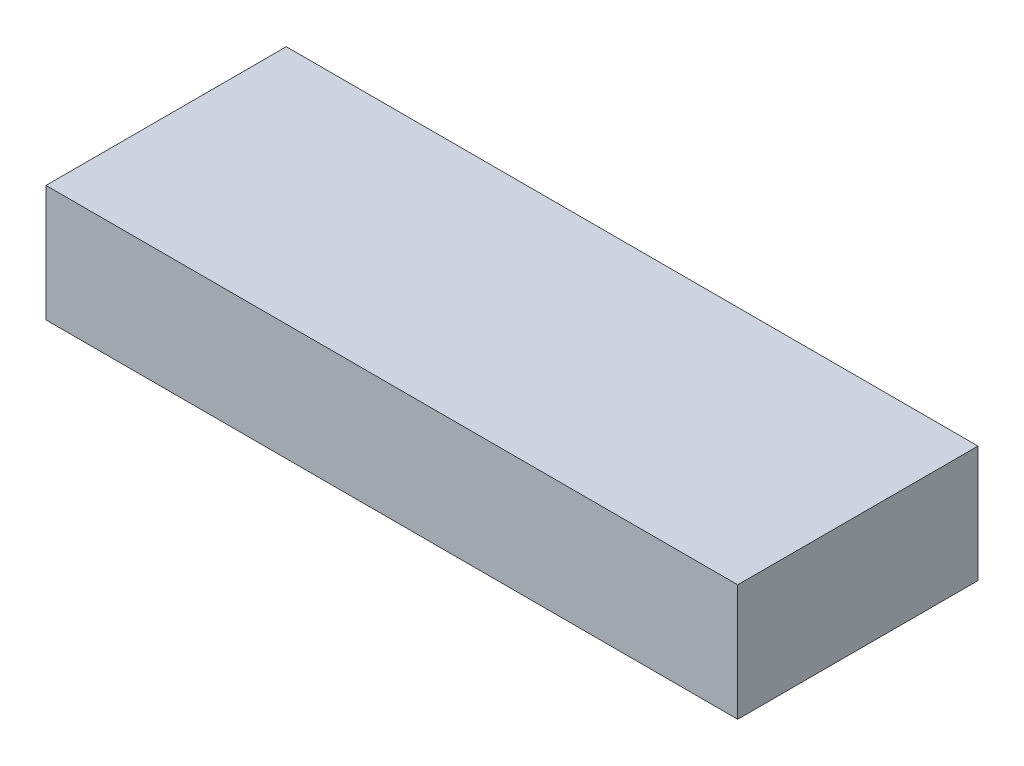
SolidWorks part; units mm, degrees
ref_plane "Front Plane" through (0, 0, 0) normal (0, 0, 1) x (1, 0, 0)
ref_plane "Top Plane" through (0, 0, 0) normal (0, 1, 0) x (1, 0, 0)
ref_plane "Right Plane" through (0, 0, 0) normal (1, 0, 0) x (0, 0, -1)
sketch "Sketch1" plane through (0, 0, 0) normal (0, 1, 0) x (1, 0, 0)
  line L1 (-23.75, -8.25) -> (23.75, -8.25)
  line L2 (-23.75, -8.25) -> (-23.75, 8.25)
  line L3 (-23.75, 8.25) -> (23.75, 8.25)
  line L4 (23.75, -8.25) -> (23.75, 8.25)
  line L5 (-23.75, -8.25) -> (23.75, 8.25) construction
  line L6 (-23.75, 8.25) -> (23.75, -8.25) construction
  point P0 (0, 0)
  dimension "D1" = 47.5
  dimension "D2" = 16.5
extrude "Boss-Extrude1" add sketch "Sketch1" along normal blind 8
